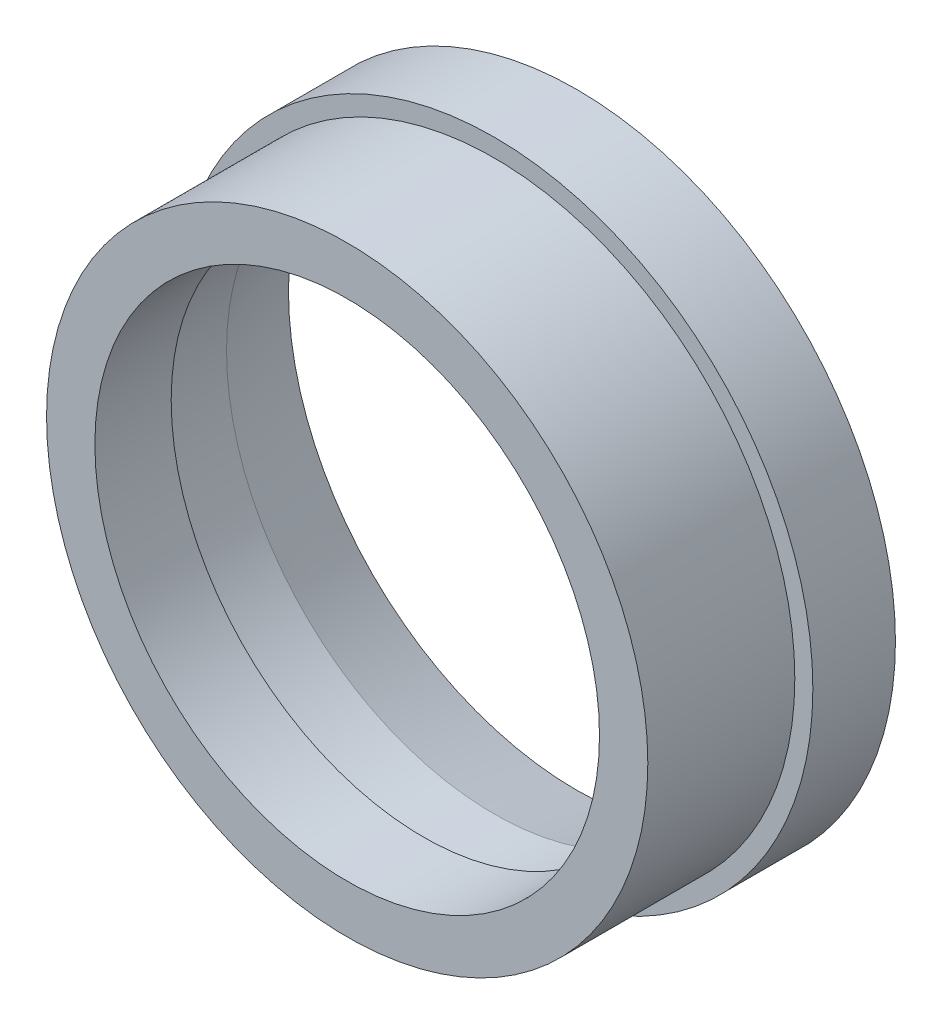
SolidWorks part; units mm, degrees
ref_plane "Front Plane" through (0, 0, 0) normal (0, 0, 1) x (1, 0, 0)
ref_plane "Top Plane" through (0, 0, 0) normal (0, 1, 0) x (1, 0, 0)
ref_plane "Right Plane" through (0, 0, 0) normal (1, 0, 0) x (0, 0, -1)
sketch "Sketch1" plane through (0, 0, 0) normal (0, 0, 1) x (1, 0, 0)
  circle A0 centre (0, 0) radius 49
  circle A1 centre (0, 0) radius 38.7985
  dimension "D1" = 77.597
  dimension "D2" = 98
extrude "Extrude1" add sketch "Sketch1" along normal blind 35.306
sketch "Sketch2" plane through (0, 0, 35.306) normal (0, 0, 1) x (1, 0, 0)
  circle A0 centre (0, 0) radius 46.228
extrude "Extrude2" cut sketch "Sketch2" against normal blind 22.606 flip side to cut
sketch "Sketch3" plane through (0, 0, 0) normal (0, 0, -1) x (-1, 0, 0)
  circle A0 centre (0, 0) radius 41.1607
  dimension "D1" = 82.3214
extrude "Extrude3" cut sketch "Sketch3" against normal blind 23.5712
chamfer "Chamfer1" distance 3.175 distance2 12.7 1 edges at (-41.1607, 0, 0)
